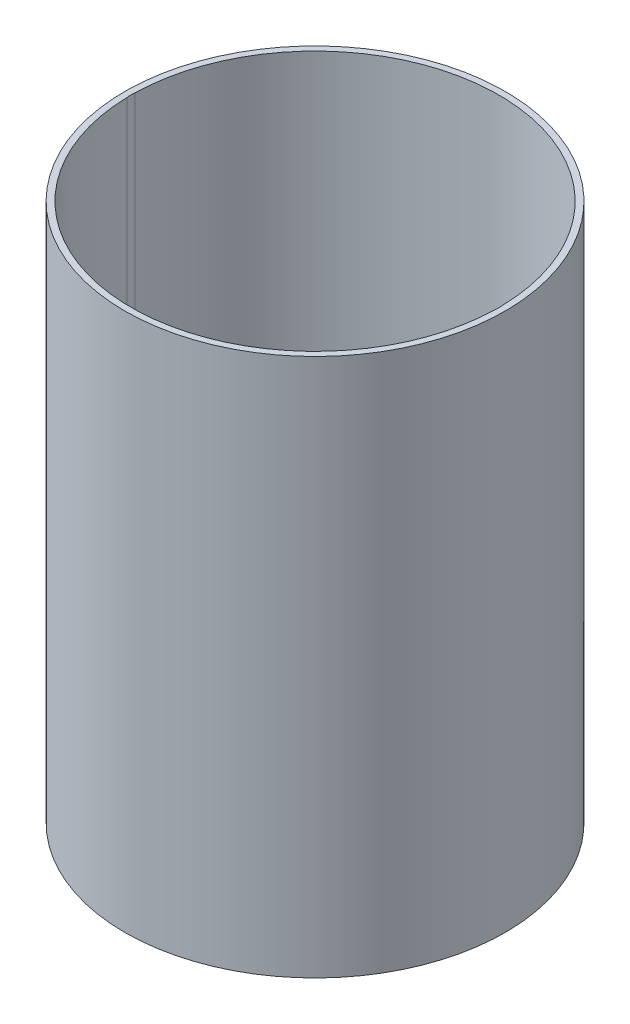
SolidWorks part; units mm, degrees
material "PET"
ref_plane "Front Plane" through (0, 0, 0) normal (0, 0, 1) x (1, 0, 0)
ref_plane "Top Plane" through (0, 0, 0) normal (0, 1, 0) x (1, 0, 0)
ref_plane "Right Plane" through (0, 0, 0) normal (1, 0, 0) x (0, 0, -1)
sketch "Sketch1" plane through (0, 0, 0) normal (0, 1, 0) x (1, 0, 0)
  circle A0 centre (0, 0) radius 92.71
  circle A1 centre (0, 0) radius 53.975
  dimension "D1" = 185.42
  dimension "D2" = 107.95
extrude "Top of Hatch" add sketch "Sketch1" along normal blind 3.302
sketch "Sketch2" plane through (0, 3.302, 0) normal (0, 1, 0) x (1, 0, 0)
  circle A0 centre (0, 0) radius 92.71
  circle A1 centre (0, 0) radius 89.662
  circle A2 centre (0, 0) radius 92.71 construction
  dimension "D1" = 3.048
extrude "Hatch Body" add sketch "Sketch2" along normal blind 259.08
sketch "Sketch3" plane through (0, 0, 0) normal (0, -1, 0) x (1, 0, 0)
  line L0 (0, 0) -> (-76.454, 0) construction
  line L1 (0, 0) -> (0, 76.902) construction
  circle A0 centre (-76.454, 0) radius 13.335
  circle A1 centre (76.454, 0) radius 13.335
  dimension "D1" = 76.454
  dimension "D2" = 26.67
extrude "Charge Tube Holes" cut sketch "Sketch3" against normal through all
sketch "Sketch4" plane through (0, 0, 0) normal (0, -1, 0) x (1, 0, 0)
  circle A0 centre (38.1, 65.9911) radius 3.81
  circle A1 centre (-38.1, 65.9911) radius 3.81
  circle A2 centre (-38.1, -65.9911) radius 3.81
  circle A3 centre (38.1, -65.9911) radius 3.81
  dimension "D1" = 76.2
  dimension "D3" = 7.62
  dimension "D4" = 76.2
  dimension "D6" = 7.62
  dimension "D9" = 7.62
  dimension "D12" = 7.62
  dimension "D2" = 38.1
  dimension "D5" = 38.1
  dimension "D7" = 76.2
  dimension "D8" = 38.1
  dimension "D10" = 76.2
  dimension "D11" = 38.1
extrude "Bolt Holes" cut sketch "Sketch4" against normal through all
sketch "Sketch 5" plane through (0, 0, 0) normal (0, -1, 0) x (1, 0, 0)
  circle A0 centre (-26.1124, 57.3248) radius 5.08
  circle A1 centre (9.1936, 61.0335) radius 5.08
  dimension "D1" = 10.16
  dimension "D2" = 10.16
  dimension "D3" = 62.992
  dimension "D4" = 61.722
  dimension "D5" = 26.1124
  dimension "D6" = 35.306
extrude "Antenna Holes " cut sketch "Sketch 5" against normal through all
